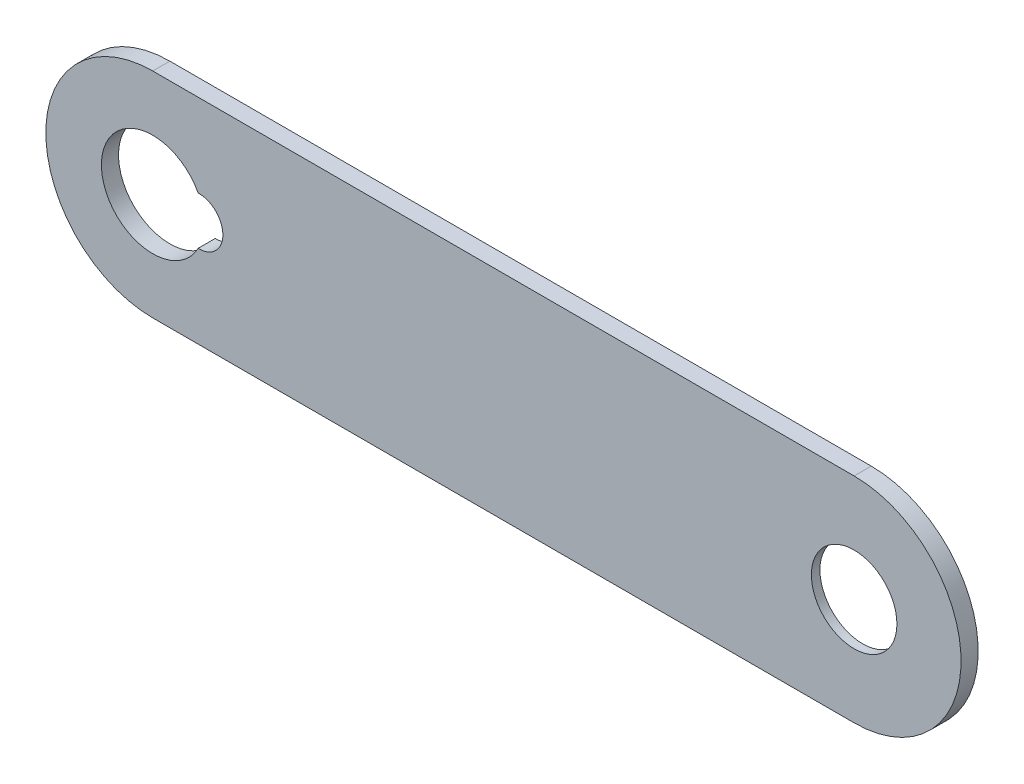
SolidWorks part; units mm, degrees
material "Custom Plastic"
ref_plane "Front Plane" through (0, 0, 0) normal (0, 0, 1) x (1, 0, 0)
ref_plane "Top Plane" through (0, 0, 0) normal (0, 1, 0) x (1, 0, 0)
ref_plane "Right Plane" through (0, 0, 0) normal (1, 0, 0) x (0, 0, -1)
sketch "Sketch1" plane through (0, 0, 0) normal (0, 0, 1) x (1, 0, 0)
  line L0 (32.5, -3.8976) -> (-49.5, -3.8976)
  line L3 (-49.5, 21.1024) -> (32.5, 21.1024)
  arc A1 (32.5, -3.8976) -> (32.5, 21.1024) centre (32.5, 8.6024) ccw
  arc A2 (-49.5, -3.8976) -> (-49.5, 21.1024) centre (-49.5, 8.6024) cw
  circle A3 centre (-49.5, 8.6024) radius 0.5
  circle A4 centre (32.5, 8.6024) radius 0.5
  point P0 (0, 0)
  dimension "D2" = 1
  dimension "D3" = 1
  dimension "D1" = 82
  dimension "D4" = 25
extrude "Boss-Extrude1" add sketch "Sketch1" along normal blind 2
sketch "Sketch3" plane through (0, 0, 0) normal (0, 0, -1) x (-1, 0, 0)
  line L0 (49.5, 8.6024) -> (49.5, 3.2024)
  line L1 (49.5, 8.6024) -> (55.5, 8.6024)
  line L2 (49.5, 8.6024) -> (46.9, 8.6024)
  arc A0 (52.2985, 3.295) -> (44.1926, 11.4009) centre (49.5, 8.6024) ccw
  arc A2 (44.1926, 11.4009) -> (44.1926, 5.8039) centre (44.1, 8.6024) ccw
  arc A3 (44.1926, 5.8039) -> (46.7015, 3.295) centre (49.5, 8.6024) ccw
  arc A4 (44.1926, 5.8039) -> (44.1926, 11.4009) centre (49.5, 8.6024) ccw
  dimension "D1" = 12
  dimension "D5" = 5.6
  dimension "D2" = 5.4
  dimension "D4" = 5.4
extrude "Cut-Extrude2" cut sketch "Sketch3" against normal blind 2
sketch "Sketch4" plane through (0, 0, 0) normal (0, 0, -1) x (-1, 0, 0)
  line L0 (-32.5, 8.6024) -> (-32.5, 14.8024)
  line L1 (-32.5, 14.8024) -> (-38.5, 14.8024)
  line L2 (-38.5, 14.8024) -> (-38.5, 2.4024)
  line L3 (-38.5, 2.4024) -> (-15.7, 2.4024)
  line L4 (-15.7, 2.4024) -> (-15.7, 14.8024)
  line L5 (-15.7, 14.8024) -> (-32.5, 14.8024)
  line L6 (-32.5, 8.6024) -> (-32.5, 2.4024)
  line L7 (-32.5, 8.6024) -> (-15.7, 8.6024)
  line L8 (-32.5, 8.6024) -> (-38.5, 8.6024)
  point P8 (0, 0)
  circle M12 centre (-32.5, 8.6024) radius 0.5
  dimension "D1" = 16.8
  dimension "D2" = 6
  dimension "D3" = 6.2
extrude "Cut-Extrude3" cut sketch "Sketch4" against normal blind 1 contours L8 L0 L1 L2 M12 | L8 L2 L3 L6 M12 | L7 L4 L5 L0 M12 | L7 L6 L3 L4 M12
sketch "Sketch5" plane through (0, 0, 2) normal (0, 0, 1) x (1, 0, 0)
  circle A0 centre (32.5, 8.6024) radius 5
  dimension "D1" = 10
extrude "Cut-Extrude4" cut sketch "Sketch5" against normal blind 10
